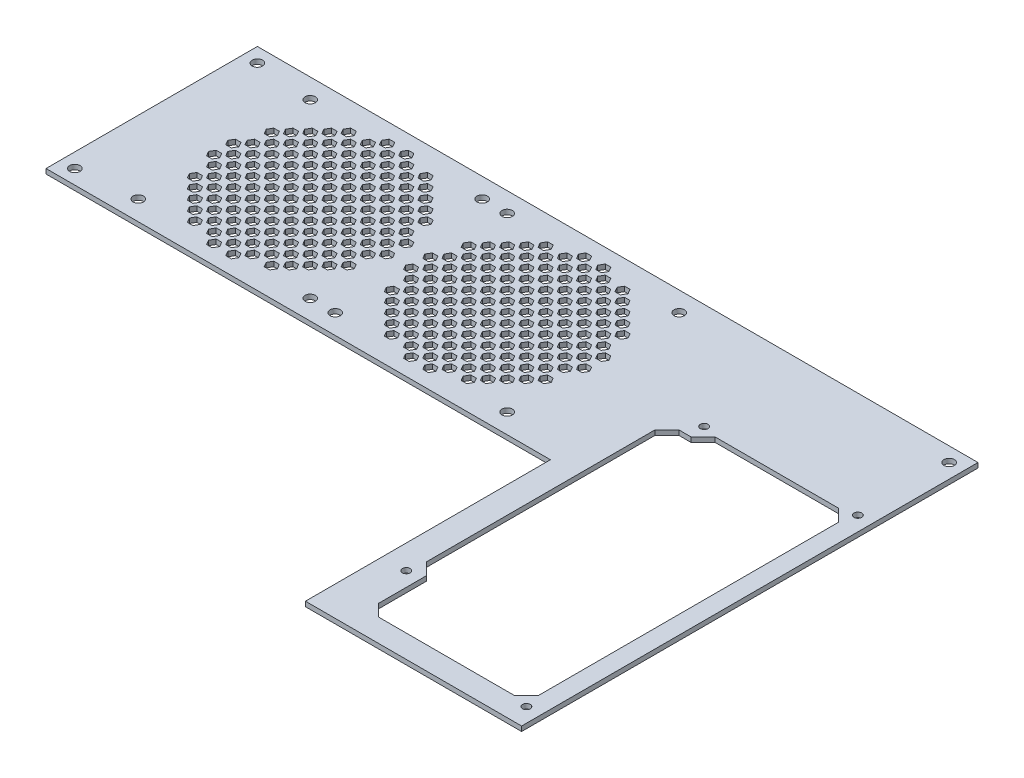
SolidWorks part; units mm, degrees
ref_plane "Front Plane" through (0, 0, 0) normal (0, 0, 1) x (1, 0, 0)
ref_plane "Top Plane" through (0, 0, 0) normal (0, 1, 0) x (1, 0, 0)
ref_plane "Right Plane" through (0, 0, 0) normal (1, 0, 0) x (0, 0, -1)
sketch "Sketch1" plane through (0, 0, 0) normal (0, 1, 0) x (1, 0, 0)
  line L0 (0, 0) -> (-210, 0)
  line L1 (-210, 0) -> (-210, 88)
  line L2 (-210, 88) -> (90, 88)
  line L3 (90, 88) -> (90, -102)
  line L4 (90, -102) -> (0, -102)
  line L5 (0, -102) -> (0, 0)
  dimension "D1" = 88
  dimension "D2" = 300
  dimension "D3" = 90
  dimension "D4" = 190
extrude "Boss-Extrude1" add sketch "Sketch1" along normal blind 2
sketch "Sketch2" plane through (0, 2, 0) normal (0, 1, 0) x (1, 0, 0)
  line L0 (21, -92.5) -> (77.5, -92.5)
  line L1 (77.5, -92.5) -> (82.5, -87.5)
  line L2 (82.5, -87.5) -> (82.5, 37.5)
  line L3 (82.5, 37.5) -> (77.5, 42.5)
  line L4 (77.5, 42.5) -> (26, 42.5)
  line L5 (26, 42.5) -> (21, 37.5)
  line L6 (21, 37.5) -> (16, 37.5)
  line L7 (16, 37.5) -> (11, 32.5)
  line L8 (11, 32.5) -> (11, -62.5)
  line L9 (11, -62.5) -> (16, -67.5)
  line L10 (16, -67.5) -> (16, -87.5)
  line L11 (16, -87.5) -> (21, -92.5)
  line L12 (0, -102) -> (90, -102) construction
  line L13 (90, -102) -> (90, 88) construction
  line L14 (82.5, -87.5) -> (82.5, -92.5) construction
  line L15 (82.5, -92.5) -> (77.5, -92.5) construction
  dimension "D1" = 9.5
  dimension "D2" = 7.5
  dimension "D3" = 5
  dimension "D4" = 135
  dimension "D5" = 71.5
  dimension "D6" = 10
  dimension "D7" = 25
extrude "Cut-Extrude1" cut sketch "Sketch2" against normal blind 3.5
sketch "Sketch4" plane through (0, 2, 0) normal (0, 1, 0) x (1, 0, 0)
  line L0 (-210, 88) -> (-210, 0) construction
  line L1 (-134.8453, 46) -> (-137.1547, 46)
  line L2 (-142.8453, 46) -> (-145.1547, 46)
  line L3 (-145.1547, 46) -> (-146.3094, 44)
  line L4 (-146.3094, 44) -> (-145.1547, 42)
  line L5 (-145.1547, 42) -> (-142.8453, 42)
  line L6 (-142.8453, 42) -> (-141.6906, 44)
  line L7 (-141.6906, 44) -> (-142.8453, 46)
  line L8 (-137.1547, 46) -> (-138.3094, 44)
  line L9 (-138.3094, 44) -> (-137.1547, 42)
  line L10 (-137.1547, 42) -> (-134.8453, 42)
  line L11 (-134.8453, 42) -> (-133.6906, 44)
  line L12 (-133.6906, 44) -> (-134.8453, 46)
  line L13 (-126.8453, 46) -> (-129.1547, 46)
  line L14 (-129.1547, 46) -> (-130.3094, 44)
  line L15 (-130.3094, 44) -> (-129.1547, 42)
  line L16 (-129.1547, 42) -> (-126.8453, 42)
  line L17 (-126.8453, 42) -> (-125.6906, 44)
  line L18 (-125.6906, 44) -> (-126.8453, 46)
  line L19 (-118.8453, 46) -> (-121.1547, 46)
  line L20 (-121.1547, 46) -> (-122.3094, 44)
  line L21 (-122.3094, 44) -> (-121.1547, 42)
  line L22 (-121.1547, 42) -> (-118.8453, 42)
  line L23 (-118.8453, 42) -> (-117.6906, 44)
  line L24 (-117.6906, 44) -> (-118.8453, 46)
  line L25 (-110.8453, 46) -> (-113.1547, 46)
  line L26 (-113.1547, 46) -> (-114.3094, 44)
  line L27 (-114.3094, 44) -> (-113.1547, 42)
  line L28 (-113.1547, 42) -> (-110.8453, 42)
  line L29 (-110.8453, 42) -> (-109.6906, 44)
  line L30 (-109.6906, 44) -> (-110.8453, 46)
  line L31 (-134.8453, 54) -> (-137.1547, 54)
  line L32 (-137.1547, 54) -> (-138.3094, 52)
  line L33 (-138.3094, 52) -> (-137.1547, 50)
  line L34 (-137.1547, 50) -> (-134.8453, 50)
  line L35 (-134.8453, 50) -> (-133.6906, 52)
  line L36 (-133.6906, 52) -> (-134.8453, 54)
  line L37 (-126.8453, 54) -> (-129.1547, 54)
  line L38 (-129.1547, 54) -> (-130.3094, 52)
  line L39 (-130.3094, 52) -> (-129.1547, 50)
  line L40 (-129.1547, 50) -> (-126.8453, 50)
  line L41 (-126.8453, 50) -> (-125.6906, 52)
  line L42 (-125.6906, 52) -> (-126.8453, 54)
  line L43 (-118.8453, 54) -> (-121.1547, 54)
  line L44 (-121.1547, 54) -> (-122.3094, 52)
  line L45 (-122.3094, 52) -> (-121.1547, 50)
  line L46 (-121.1547, 50) -> (-118.8453, 50)
  line L47 (-118.8453, 50) -> (-117.6906, 52)
  line L48 (-117.6906, 52) -> (-118.8453, 54)
  line L49 (-110.8453, 54) -> (-113.1547, 54)
  line L50 (-113.1547, 54) -> (-114.3094, 52)
  line L51 (-114.3094, 52) -> (-113.1547, 50)
  line L52 (-113.1547, 50) -> (-110.8453, 50)
  line L53 (-110.8453, 50) -> (-109.6906, 52)
  line L54 (-109.6906, 52) -> (-110.8453, 54)
  line L55 (-134.8453, 62) -> (-137.1547, 62)
  line L56 (-137.1547, 62) -> (-138.3094, 60)
  line L57 (-138.3094, 60) -> (-137.1547, 58)
  line L58 (-137.1547, 58) -> (-134.8453, 58)
  line L59 (-134.8453, 58) -> (-133.6906, 60)
  line L60 (-133.6906, 60) -> (-134.8453, 62)
  line L61 (-126.8453, 62) -> (-129.1547, 62)
  line L62 (-129.1547, 62) -> (-130.3094, 60)
  line L63 (-130.3094, 60) -> (-129.1547, 58)
  line L64 (-129.1547, 58) -> (-126.8453, 58)
  line L65 (-126.8453, 58) -> (-125.6906, 60)
  line L66 (-125.6906, 60) -> (-126.8453, 62)
  line L67 (-118.8453, 62) -> (-121.1547, 62)
  line L68 (-121.1547, 62) -> (-122.3094, 60)
  line L69 (-122.3094, 60) -> (-121.1547, 58)
  line L70 (-121.1547, 58) -> (-118.8453, 58)
  line L71 (-118.8453, 58) -> (-117.6906, 60)
  line L72 (-117.6906, 60) -> (-118.8453, 62)
  line L73 (-110.8453, 62) -> (-113.1547, 62)
  line L74 (-113.1547, 62) -> (-114.3094, 60)
  line L75 (-114.3094, 60) -> (-113.1547, 58)
  line L76 (-113.1547, 58) -> (-110.8453, 58)
  line L77 (-110.8453, 58) -> (-109.6906, 60)
  line L78 (-109.6906, 60) -> (-110.8453, 62)
  line L79 (-134.8453, 70) -> (-137.1547, 70)
  line L80 (-137.1547, 70) -> (-138.3094, 68)
  line L81 (-138.3094, 68) -> (-137.1547, 66)
  line L82 (-137.1547, 66) -> (-134.8453, 66)
  line L83 (-134.8453, 66) -> (-133.6906, 68)
  line L84 (-133.6906, 68) -> (-134.8453, 70)
  line L85 (-126.8453, 70) -> (-129.1547, 70)
  line L86 (-129.1547, 70) -> (-130.3094, 68)
  line L87 (-130.3094, 68) -> (-129.1547, 66)
  line L88 (-129.1547, 66) -> (-126.8453, 66)
  line L89 (-126.8453, 66) -> (-125.6906, 68)
  line L90 (-125.6906, 68) -> (-126.8453, 70)
  line L91 (-118.8453, 70) -> (-121.1547, 70)
  line L92 (-121.1547, 70) -> (-122.3094, 68)
  line L93 (-122.3094, 68) -> (-121.1547, 66)
  line L94 (-121.1547, 66) -> (-118.8453, 66)
  line L95 (-118.8453, 66) -> (-117.6906, 68)
  line L96 (-117.6906, 68) -> (-118.8453, 70)
  line L103 (-134.8453, 78) -> (-137.1547, 78)
  line L104 (-137.1547, 78) -> (-138.3094, 76)
  line L105 (-138.3094, 76) -> (-137.1547, 74)
  line L106 (-137.1547, 74) -> (-134.8453, 74)
  line L107 (-134.8453, 74) -> (-133.6906, 76)
  line L108 (-133.6906, 76) -> (-134.8453, 78)
  line L109 (-126.8453, 78) -> (-129.1547, 78)
  line L110 (-129.1547, 78) -> (-130.3094, 76)
  line L111 (-130.3094, 76) -> (-129.1547, 74)
  line L112 (-129.1547, 74) -> (-126.8453, 74)
  line L113 (-126.8453, 74) -> (-125.6906, 76)
  line L114 (-125.6906, 76) -> (-126.8453, 78)
  line L127 (-142.8453, 54) -> (-145.1547, 54)
  line L128 (-145.1547, 54) -> (-146.3094, 52)
  line L129 (-146.3094, 52) -> (-145.1547, 50)
  line L130 (-145.1547, 50) -> (-142.8453, 50)
  line L131 (-142.8453, 50) -> (-141.6906, 52)
  line L132 (-141.6906, 52) -> (-142.8453, 54)
  line L133 (-142.8453, 62) -> (-145.1547, 62)
  line L134 (-145.1547, 62) -> (-146.3094, 60)
  line L135 (-146.3094, 60) -> (-145.1547, 58)
  line L136 (-145.1547, 58) -> (-142.8453, 58)
  line L137 (-142.8453, 58) -> (-141.6906, 60)
  line L138 (-141.6906, 60) -> (-142.8453, 62)
  line L139 (-142.8453, 70) -> (-145.1547, 70)
  line L140 (-145.1547, 70) -> (-146.3094, 68)
  line L141 (-146.3094, 68) -> (-145.1547, 66)
  line L142 (-145.1547, 66) -> (-142.8453, 66)
  line L143 (-142.8453, 66) -> (-141.6906, 68)
  line L144 (-141.6906, 68) -> (-142.8453, 70)
  line L145 (-142.8453, 78) -> (-145.1547, 78)
  line L146 (-145.1547, 78) -> (-146.3094, 76)
  line L147 (-146.3094, 76) -> (-145.1547, 74)
  line L148 (-145.1547, 74) -> (-142.8453, 74)
  line L149 (-142.8453, 74) -> (-141.6906, 76)
  line L150 (-141.6906, 76) -> (-142.8453, 78)
  line L151 (-118.8453, 78) -> (-121.1547, 78) [skipped]
  line L152 (-121.1547, 78) -> (-122.3094, 76) [skipped]
  line L153 (-122.3094, 76) -> (-121.1547, 74) [skipped]
  line L154 (-121.1547, 74) -> (-118.8453, 74) [skipped]
  line L155 (-118.8453, 74) -> (-117.6906, 76) [skipped]
  line L156 (-117.6906, 76) -> (-118.8453, 78) [skipped]
  line L157 (-110.8453, 78) -> (-113.1547, 78) [skipped]
  line L158 (-113.1547, 78) -> (-114.3094, 76) [skipped]
  line L159 (-114.3094, 76) -> (-113.1547, 74) [skipped]
  line L160 (-113.1547, 74) -> (-110.8453, 74) [skipped]
  line L161 (-110.8453, 74) -> (-109.6906, 76) [skipped]
  line L162 (-109.6906, 76) -> (-110.8453, 78) [skipped]
  line L163 (-110.8453, 66) -> (-109.6906, 68) [skipped]
  line L164 (-110.8453, 70) -> (-113.1547, 70) [skipped]
  line L165 (-113.1547, 70) -> (-114.3094, 68) [skipped]
  line L166 (-114.3094, 68) -> (-113.1547, 66) [skipped]
  line L167 (-113.1547, 66) -> (-110.8453, 66) [skipped]
  line L168 (-109.6906, 68) -> (-110.8453, 70) [skipped]
  circle A0 centre (-144, 44) radius 37.5 construction
  circle A1 centre (-144, 44) radius 2 construction
  point P5 (-210, 44)
  dimension "D1" = 75
  dimension "D3" = 4
  dimension "D2" = 66
  dimension "D4" = 8
  dimension "D5" = 8
  dimension "D6" = 5
  dimension "D7" = 5
extrude "Cut-Extrude3" cut sketch "Sketch4" against normal up to next (2 mm away)
sketch "Sketch5" plane through (0, 2, 0) normal (0, 1, 0) x (1, 0, 0)
  line L0 (-129.6906, 48) -> (-130.8453, 50)
  line L1 (-137.6906, 48) -> (-138.8453, 50)
  line L2 (-138.8453, 50) -> (-141.1547, 50)
  line L3 (-141.1547, 50) -> (-142.3094, 48)
  line L4 (-142.3094, 48) -> (-141.1547, 46)
  line L5 (-141.1547, 46) -> (-138.8453, 46)
  line L6 (-138.8453, 46) -> (-137.6906, 48)
  line L7 (-130.8453, 50) -> (-133.1547, 50)
  line L8 (-133.1547, 50) -> (-134.3094, 48)
  line L9 (-134.3094, 48) -> (-133.1547, 46)
  line L10 (-133.1547, 46) -> (-130.8453, 46)
  line L11 (-130.8453, 46) -> (-129.6906, 48)
  line L12 (-121.6906, 48) -> (-122.8453, 50)
  line L13 (-122.8453, 50) -> (-125.1547, 50)
  line L14 (-125.1547, 50) -> (-126.3094, 48)
  line L15 (-126.3094, 48) -> (-125.1547, 46)
  line L16 (-125.1547, 46) -> (-122.8453, 46)
  line L17 (-122.8453, 46) -> (-121.6906, 48)
  line L18 (-113.6906, 48) -> (-114.8453, 50)
  line L19 (-114.8453, 50) -> (-117.1547, 50)
  line L20 (-117.1547, 50) -> (-118.3094, 48)
  line L21 (-118.3094, 48) -> (-117.1547, 46)
  line L22 (-117.1547, 46) -> (-114.8453, 46)
  line L23 (-114.8453, 46) -> (-113.6906, 48)
  line L24 (-105.6906, 48) -> (-106.8453, 50)
  line L25 (-106.8453, 50) -> (-109.1547, 50)
  line L26 (-109.1547, 50) -> (-110.3094, 48)
  line L27 (-110.3094, 48) -> (-109.1547, 46)
  line L28 (-109.1547, 46) -> (-106.8453, 46)
  line L29 (-106.8453, 46) -> (-105.6906, 48)
  line L30 (-129.6906, 56) -> (-130.8453, 58)
  line L31 (-130.8453, 58) -> (-133.1547, 58)
  line L32 (-133.1547, 58) -> (-134.3094, 56)
  line L33 (-134.3094, 56) -> (-133.1547, 54)
  line L34 (-133.1547, 54) -> (-130.8453, 54)
  line L35 (-130.8453, 54) -> (-129.6906, 56)
  line L36 (-121.6906, 56) -> (-122.8453, 58)
  line L37 (-122.8453, 58) -> (-125.1547, 58)
  line L38 (-125.1547, 58) -> (-126.3094, 56)
  line L39 (-126.3094, 56) -> (-125.1547, 54)
  line L40 (-125.1547, 54) -> (-122.8453, 54)
  line L41 (-122.8453, 54) -> (-121.6906, 56)
  line L42 (-113.6906, 56) -> (-114.8453, 58)
  line L43 (-114.8453, 58) -> (-117.1547, 58)
  line L44 (-117.1547, 58) -> (-118.3094, 56)
  line L45 (-118.3094, 56) -> (-117.1547, 54)
  line L46 (-117.1547, 54) -> (-114.8453, 54)
  line L47 (-114.8453, 54) -> (-113.6906, 56)
  line L54 (-129.6906, 64) -> (-130.8453, 66)
  line L55 (-130.8453, 66) -> (-133.1547, 66)
  line L56 (-133.1547, 66) -> (-134.3094, 64)
  line L57 (-134.3094, 64) -> (-133.1547, 62)
  line L58 (-133.1547, 62) -> (-130.8453, 62)
  line L59 (-130.8453, 62) -> (-129.6906, 64)
  line L60 (-121.6906, 64) -> (-122.8453, 66)
  line L61 (-122.8453, 66) -> (-125.1547, 66)
  line L62 (-125.1547, 66) -> (-126.3094, 64)
  line L63 (-126.3094, 64) -> (-125.1547, 62)
  line L64 (-125.1547, 62) -> (-122.8453, 62)
  line L65 (-122.8453, 62) -> (-121.6906, 64)
  line L66 (-113.6906, 64) -> (-114.8453, 66)
  line L67 (-114.8453, 66) -> (-117.1547, 66)
  line L68 (-117.1547, 66) -> (-118.3094, 64)
  line L69 (-118.3094, 64) -> (-117.1547, 62)
  line L70 (-117.1547, 62) -> (-114.8453, 62)
  line L71 (-114.8453, 62) -> (-113.6906, 64)
  line L78 (-129.6906, 72) -> (-130.8453, 74)
  line L79 (-130.8453, 74) -> (-133.1547, 74)
  line L80 (-133.1547, 74) -> (-134.3094, 72)
  line L81 (-134.3094, 72) -> (-133.1547, 70)
  line L82 (-133.1547, 70) -> (-130.8453, 70)
  line L83 (-130.8453, 70) -> (-129.6906, 72)
  line L84 (-121.6906, 72) -> (-122.8453, 74)
  line L85 (-122.8453, 74) -> (-125.1547, 74)
  line L86 (-125.1547, 74) -> (-126.3094, 72)
  line L87 (-126.3094, 72) -> (-125.1547, 70)
  line L88 (-125.1547, 70) -> (-122.8453, 70)
  line L89 (-122.8453, 70) -> (-121.6906, 72)
  line L126 (-137.6906, 56) -> (-138.8453, 58)
  line L127 (-138.8453, 58) -> (-141.1547, 58)
  line L128 (-141.1547, 58) -> (-142.3094, 56)
  line L129 (-142.3094, 56) -> (-141.1547, 54)
  line L130 (-141.1547, 54) -> (-138.8453, 54)
  line L131 (-138.8453, 54) -> (-137.6906, 56)
  line L132 (-137.6906, 64) -> (-138.8453, 66)
  line L133 (-138.8453, 66) -> (-141.1547, 66)
  line L134 (-141.1547, 66) -> (-142.3094, 64)
  line L135 (-142.3094, 64) -> (-141.1547, 62)
  line L136 (-141.1547, 62) -> (-138.8453, 62)
  line L137 (-138.8453, 62) -> (-137.6906, 64)
  line L138 (-137.6906, 72) -> (-138.8453, 74)
  line L139 (-138.8453, 74) -> (-141.1547, 74)
  line L140 (-141.1547, 74) -> (-142.3094, 72)
  line L141 (-142.3094, 72) -> (-141.1547, 70)
  line L142 (-141.1547, 70) -> (-138.8453, 70)
  line L143 (-138.8453, 70) -> (-137.6906, 72)
  line L144 (-137.6906, 80) -> (-138.8453, 82)
  line L145 (-138.8453, 82) -> (-141.1547, 82)
  line L146 (-141.1547, 82) -> (-142.3094, 80)
  line L147 (-142.3094, 80) -> (-141.1547, 78)
  line L148 (-141.1547, 78) -> (-138.8453, 78)
  line L149 (-138.8453, 78) -> (-137.6906, 80)
  line L150 (-121.6906, 80) -> (-122.8453, 82) [skipped]
  line L151 (-122.8453, 82) -> (-125.1547, 82) [skipped]
  line L152 (-125.1547, 82) -> (-126.3094, 80) [skipped]
  line L153 (-126.3094, 80) -> (-125.1547, 78) [skipped]
  line L154 (-125.1547, 78) -> (-122.8453, 78) [skipped]
  line L155 (-122.8453, 78) -> (-121.6906, 80) [skipped]
  line L156 (-113.6906, 80) -> (-114.8453, 82) [skipped]
  line L157 (-114.8453, 82) -> (-117.1547, 82) [skipped]
  line L158 (-117.1547, 82) -> (-118.3094, 80) [skipped]
  line L159 (-118.3094, 80) -> (-117.1547, 78) [skipped]
  line L160 (-117.1547, 78) -> (-114.8453, 78) [skipped]
  line L161 (-114.8453, 78) -> (-113.6906, 80) [skipped]
  line L162 (-105.6906, 80) -> (-106.8453, 82) [skipped]
  line L163 (-106.8453, 82) -> (-109.1547, 82) [skipped]
  line L164 (-109.1547, 82) -> (-110.3094, 80) [skipped]
  line L165 (-110.3094, 80) -> (-109.1547, 78) [skipped]
  line L166 (-109.1547, 78) -> (-106.8453, 78) [skipped]
  line L167 (-106.8453, 78) -> (-105.6906, 80) [skipped]
  line L168 (-113.6906, 72) -> (-114.8453, 74) [skipped]
  line L169 (-114.8453, 74) -> (-117.1547, 74) [skipped]
  line L170 (-117.1547, 74) -> (-118.3094, 72) [skipped]
  line L171 (-118.3094, 72) -> (-117.1547, 70) [skipped]
  line L172 (-117.1547, 70) -> (-114.8453, 70) [skipped]
  line L173 (-114.8453, 70) -> (-113.6906, 72) [skipped]
  line L174 (-105.6906, 72) -> (-106.8453, 74) [skipped]
  line L175 (-106.8453, 74) -> (-109.1547, 74) [skipped]
  line L176 (-109.1547, 74) -> (-110.3094, 72) [skipped]
  line L177 (-110.3094, 72) -> (-109.1547, 70) [skipped]
  line L178 (-109.1547, 70) -> (-106.8453, 70) [skipped]
  line L179 (-106.8453, 70) -> (-105.6906, 72) [skipped]
  line L180 (-105.6906, 64) -> (-106.8453, 66) [skipped]
  line L181 (-106.8453, 66) -> (-109.1547, 66) [skipped]
  line L182 (-109.1547, 66) -> (-110.3094, 64) [skipped]
  line L183 (-110.3094, 64) -> (-109.1547, 62) [skipped]
  line L184 (-109.1547, 62) -> (-106.8453, 62) [skipped]
  line L185 (-106.8453, 62) -> (-105.6906, 64) [skipped]
  line L186 (-129.6906, 80) -> (-130.8453, 82) [skipped]
  line L187 (-130.8453, 82) -> (-133.1547, 82) [skipped]
  line L188 (-133.1547, 82) -> (-134.3094, 80) [skipped]
  line L189 (-134.3094, 80) -> (-133.1547, 78) [skipped]
  line L190 (-133.1547, 78) -> (-130.8453, 78) [skipped]
  line L191 (-130.8453, 78) -> (-129.6906, 80) [skipped]
  line L192 (-105.6906, 56) -> (-106.8453, 58) [skipped]
  line L193 (-106.8453, 58) -> (-109.1547, 58) [skipped]
  line L194 (-109.1547, 58) -> (-110.3094, 56) [skipped]
  line L195 (-110.3094, 56) -> (-109.1547, 54) [skipped]
  line L196 (-109.1547, 54) -> (-106.8453, 54) [skipped]
  line L197 (-106.8453, 54) -> (-105.6906, 56) [skipped]
  circle A0 centre (-140, 48) radius 2 construction
  circle A1 centre (-144, 44) radius 2 construction
  dimension "D1" = 4
  dimension "D2" = 4
  dimension "D5" = 8
  dimension "D6" = 8
  dimension "D3" = 5
  dimension "D4" = 5
extrude "Cut-Extrude4" cut sketch "Sketch5" against normal up to next (2 mm away)
ref_plane "Plane1" through (0, 0, -44) normal (0, 0, -1) x (-1, 0, 0)
ref_plane "Plane2" through (-144, 0, 0) normal (-1, 0, 0) x (0, 0, 1)
mirror "Mirror1" about plane through (-144, 0, 0) normal (-1, 0, 0) of "Cut-Extrude4", "Cut-Extrude3"
mirror "Mirror2" about plane through (0, 0, -44) normal (0, 0, -1) of "Mirror1", "Cut-Extrude3", "Cut-Extrude4"
pattern_linear "LPattern1" count 2 spacing 82 along (1, 0, 0) of "Mirror2", "Cut-Extrude3", "Cut-Extrude4", "Mirror1"
hole_wizard "M4 Clearance Hole1" positions "Sketch6" profile "Sketch7" hole size "M4" standard "DIN"
sketch "Sketch6" plane through (0, 2, 0) normal (0, 1, 0) x (1, 0, 0)
  line L1 (-179.8, 8.2) -> (-108.2, 8.2) construction
  line L2 (-179.8, 8.2) -> (-179.8, 79.8) construction
  line L3 (-179.8, 79.8) -> (-108.2, 79.8) construction
  line L4 (-108.2, 8.2) -> (-108.2, 79.8) construction
  line L5 (-179.8, 8.2) -> (-108.2, 79.8) construction
  line L6 (-179.8, 79.8) -> (-108.2, 8.2) construction
  line L8 (-97.8, 8.2) -> (-26.2, 8.2) construction
  line L9 (-97.8, 8.2) -> (-97.8, 79.8) construction
  line L10 (-97.8, 79.8) -> (-26.2, 79.8) construction
  line L11 (-26.2, 8.2) -> (-26.2, 79.8) construction
  line L12 (-97.8, 8.2) -> (-26.2, 79.8) construction
  line L13 (-97.8, 79.8) -> (-26.2, 8.2) construction
  line L14 (-142.8453, 46) -> (-145.1547, 46) construction
  line L15 (-60.8453, 46) -> (-63.1547, 46) construction
  point P2 (-108.2, 79.8)
  point P67 (-179.8, 8.2)
  point P68 (-179.8, 79.8)
  point P69 (-108.2, 8.2)
  point P72 (-26.2, 79.8)
  point P121 (-97.8, 8.2)
  point P122 (-97.8, 79.8)
  point P123 (-26.2, 8.2)
  point P127 (-144, 44)
  point P128 (-62, 44)
  point P132 (-144, 46)
  point P135 (-62, 46)
  dimension "D1" = 71.6
sketch "Sketch7" plane through (-108.2, 2, -79.8) normal (1, 0, 0) x (0, 0, 1)
  line L0 (0, 0) -> (0, 2)
  line L1 (0, 2) -> (2.15, 2)
  line L2 (2.15, 2) -> (2.15, 0)
  line L5 (2.15, 0) -> (0, 0)
  line L11 (0, -6.35) -> (0, 107.95) construction
  dimension "Thru Hole Dia." = 4.3
  dimension "Thru Hole Depth" = 2
hole_wizard "M3 Clearance Hole1" positions "Sketch8" profile "Sketch9" hole size "M3" standard "DIN"
sketch "Sketch8" plane through (0, 2, 0) normal (0, 1, 0) x (1, 0, 0)
  line L0 (90, -102) -> (90, 88) construction
  line L1 (0, -102) -> (90, -102) construction
  point P0 (20, 44)
  point P2 (84, 44)
  point P4 (84, -94)
  point P6 (10, -70)
  dimension "D1" = 64
  dimension "D2" = 74
  dimension "D3" = 138
  dimension "D4" = 114
  dimension "D5" = 6
  dimension "D6" = 8
sketch "Sketch9" plane through (20, 2, -44) normal (1, 0, 0) x (0, 0, 1)
  line L0 (0, 0) -> (0, 2)
  line L1 (0, 2) -> (1.6, 2)
  line L2 (1.6, 2) -> (1.6, 0)
  line L5 (1.6, 0) -> (0, 0)
  line L11 (0, -6.35) -> (0, 107.95) construction
  dimension "Thru Hole Dia." = 3.2
  dimension "Thru Hole Depth" = 2
hole_wizard "M4 Clearance Hole2" positions "Sketch10" profile "Sketch11" hole size "M4" standard "DIN"
sketch "Sketch10" plane through (0, 2, 0) normal (0, 1, 0) x (1, 0, 0)
  line L0 (-210, 0) -> (0, 0) construction
  line L1 (-210, 88) -> (-210, 0) construction
  line L2 (90, -102) -> (90, 88) construction
  line L3 (90, 88) -> (-210, 88) construction
  point P0 (-204, 82)
  point P2 (-204, 6)
  point P4 (84, 82)
  point P7 (0, 0)
  point P8 (0, 0)
  dimension "D1" = 6
  dimension "D2" = 6
  dimension "D3" = 6
  dimension "D4" = 6
sketch "Sketch11" plane through (-204, 2, -82) normal (1, 0, 0) x (0, 0, 1)
  line L0 (0, 0) -> (0, 2)
  line L1 (0, 2) -> (2.15, 2)
  line L2 (2.15, 2) -> (2.15, 0)
  line L5 (2.15, 0) -> (0, 0)
  line L11 (0, -6.35) -> (0, 107.95) construction
  dimension "Thru Hole Dia." = 4.3
  dimension "Thru Hole Depth" = 2
